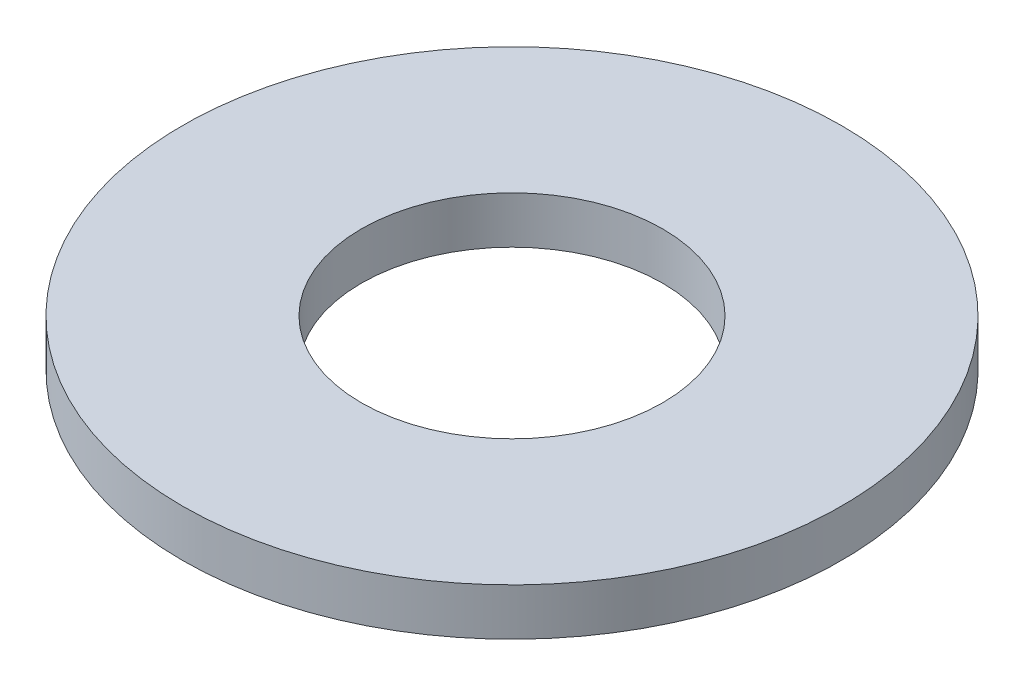
SolidWorks part; units mm, degrees
material "1.4057 (X17CrNi16-2)"
ref_plane "Plano frontal" through (0, 0, 0) normal (0, 0, 1) x (1, 0, 0)
ref_plane "Plano superior" through (0, 0, 0) normal (0, 1, 0) x (1, 0, 0)
ref_plane "Plano direito" through (0, 0, 0) normal (1, 0, 0) x (0, 0, -1)
sketch "Esboço1" plane through (0, 0, 0) normal (0, 1, 0) x (1, 0, 0)
  circle A0 centre (0, 0) radius 3.5
  circle A1 centre (0, 0) radius 1.6
  dimension "D1" = 3.2
  dimension "D2" = 7
extrude "Ressalto-extrusão1" add sketch "Esboço1" along normal blind 0.5
